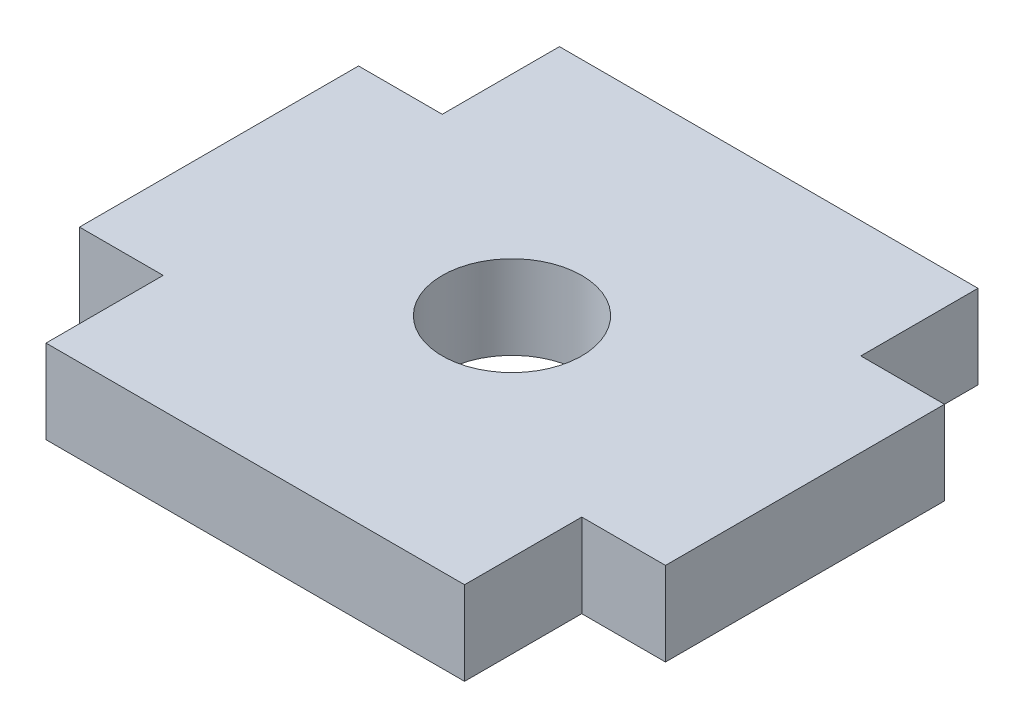
SolidWorks part; units mm, degrees
material "MDF"
ref_plane "Plano frontal" through (0, 0, 0) normal (0, 0, 1) x (1, 0, 0)
ref_plane "Plano superior" through (0, 0, 0) normal (0, 1, 0) x (1, 0, 0)
ref_plane "Plano direito" through (0, 0, 0) normal (1, 0, 0) x (0, 0, -1)
ref_plane "Plano1" through (0, 10, 0) normal (0, -1, 0) x (1, 0, 0)
sketch "Esboço1" plane through (0, 10, 0) normal (0, -1, 0) x (1, 0, 0)
  line L0 (-61.5, -9.1999) -> (-61.5, -5)
  line L1 (-61.5, -5) -> (-58.5, -5)
  line L2 (-58.5, -5) -> (-58.5, 5)
  line L3 (-58.5, 5) -> (-61.5, 5)
  line L4 (-61.5, 5) -> (-61.5, 9.1999)
  line L5 (-61.5, 9.1999) -> (-76.5, 9.1999)
  line L6 (-76.5, 9.1999) -> (-76.5, 5)
  line L7 (-76.5, 5) -> (-79.5, 5)
  line L8 (-79.5, 5) -> (-79.5, -5)
  line L9 (-79.5, -5) -> (-76.5, -5)
  line L10 (-76.5, -5) -> (-76.5, -9.1999)
  line L11 (-76.5, -9.1999) -> (-61.5, -9.1999)
  line L12 (-61.5, 9.1999) -> (-76.5, -9.1999) construction
  line L13 (-61.5, -9.1999) -> (-76.5, 9.1999) construction
  circle A0 centre (-69, 0) radius 2.5
  dimension "D7" = 5
  dimension "D1" = 15
  dimension "D2" = 4.1999
  dimension "D3" = 4.1999
  dimension "D4" = 3
  dimension "D5" = 10
  dimension "D6" = 3
extrude "Ressalto-extrusão1" add sketch "Esboço1" against normal blind 3
